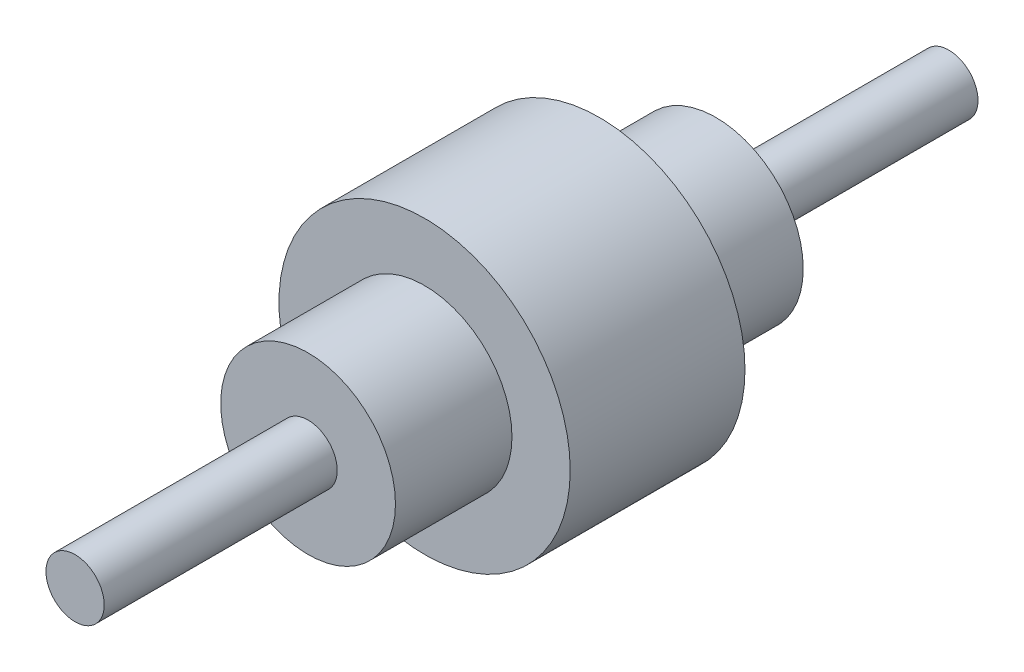
SolidWorks part; units mm, degrees
ref_plane "Front Plane" through (0, 0, 0) normal (0, 0, 1) x (1, 0, 0)
ref_plane "Top Plane" through (0, 0, 0) normal (0, 1, 0) x (1, 0, 0)
ref_plane "Right Plane" through (0, 0, 0) normal (1, 0, 0) x (0, 0, -1)
sketch "Sketch1" plane through (0, 0, 0) normal (0, 1, 0) x (1, 0, 0)
  line L0 (0, 0) -> (0, 300) construction
  line L1 (0, 300) -> (10, 300)
  line L2 (10, 300) -> (10, 220)
  line L3 (10, 220) -> (30, 220)
  line L4 (30, 220) -> (30, 180)
  line L5 (30, 180) -> (50, 180)
  line L6 (50, 180) -> (50, 120)
  line L7 (50, 120) -> (30, 120)
  line L8 (30, 120) -> (30, 80)
  line L9 (30, 80) -> (10, 80)
  line L10 (10, 80) -> (10, 0)
  line L11 (10, 0) -> (0, 0)
  line L12 (0, 300) -> (0, 0)
  dimension "D1" = 300
  dimension "D2" = 10
  dimension "D3" = 80
  dimension "D4" = 40
  dimension "D5" = 40
  dimension "D6" = 80
  dimension "D7" = 10
  dimension "D8" = 30
  dimension "D9" = 50
  dimension "D10" = 30
revolve "Revolve1" add sketch "Sketch1" angle 360 about L0
